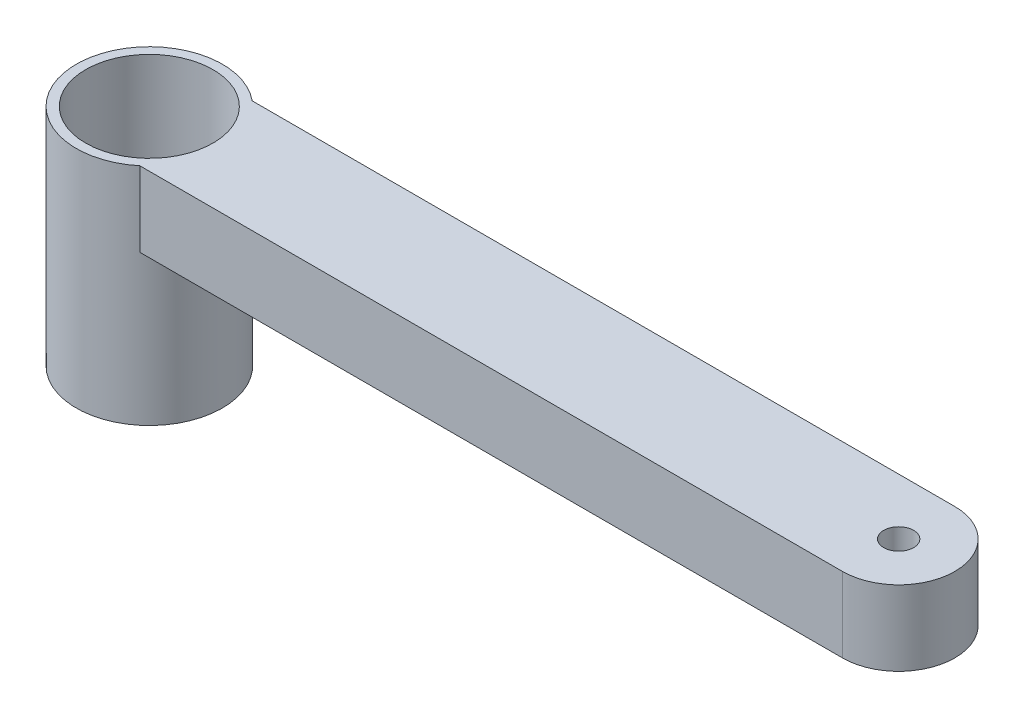
SolidWorks part; units mm, degrees
ref_plane "Front Plane" through (0, 0, 0) normal (0, 0, 1) x (1, 0, 0)
ref_plane "Top Plane" through (0, 0, 0) normal (0, 1, 0) x (1, 0, 0)
ref_plane "Right Plane" through (0, 0, 0) normal (1, 0, 0) x (0, 0, -1)
sketch "Sketch2" plane through (0, 0, 0) normal (0, 1, 0) x (1, 0, 0)
  line L0 (0, 0) -> (100, 0) construction
  line L1 (0, 7.5) -> (100, 7.5)
  line L2 (0, -7.5) -> (100, -7.5)
  arc A0 (0, 7.5) -> (0, -7.5) centre (0, 0) ccw
  arc A1 (100, -7.5) -> (100, 7.5) centre (100, 0) ccw
  circle A2 centre (0, 0) radius 2.5
  circle A3 centre (100, 0) radius 2
  point P3 (50, 0)
  dimension "D2" = 5
  dimension "D4" = 4
  dimension "D1" = 100
  dimension "D3" = 15
extrude "Boss-Extrude1" add sketch "Sketch2" along normal blind 10
sketch "Sketch3" plane through (0, 10, 0) normal (0, -1, 0) x (-1, 0, 0)
  circle A0 centre (0, 0) radius 9.75
  dimension "D1" = 19.5
extrude "Boss-Extrude2" add sketch "Sketch3" along normal blind 30
sketch "Sketch4" plane through (0, 10, 0) normal (0, 1, 0) x (1, 0, 0)
  circle A0 centre (0, 0) radius 8.5
  dimension "D1" = 17
extrude "Cut-Extrude1" cut sketch "Sketch4" against normal up to next
